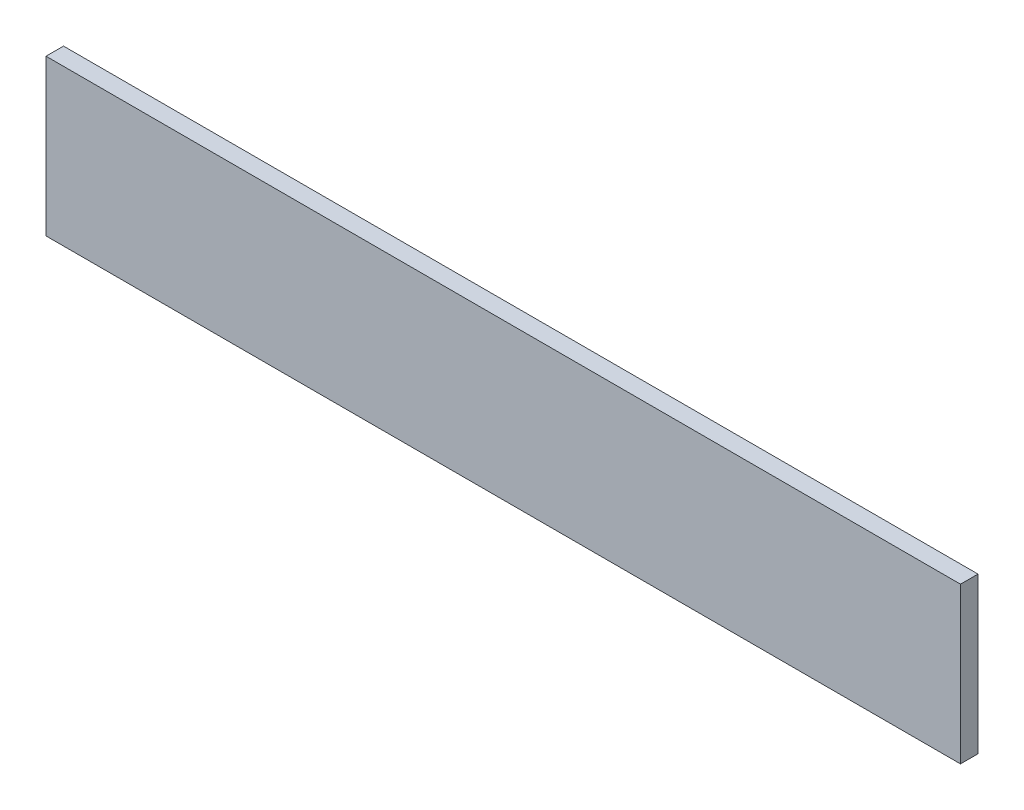
SolidWorks part; units mm, degrees
ref_plane "Płaszczyzna przednia" through (0, 0, 0) normal (0, 0, 1) x (1, 0, 0)
ref_plane "Płaszczyzna górna" through (0, 0, 0) normal (0, 1, 0) x (1, 0, 0)
ref_plane "Płaszczyzna prawa" through (0, 0, 0) normal (1, 0, 0) x (0, 0, -1)
sketch "Szkic1" plane through (0, 0, 0) normal (0, 0, 1) x (1, 0, 0)
  line L1 (0, 0) -> (470, 0)
  line L2 (0, 0) -> (0, 80)
  line L3 (0, 80) -> (470, 80)
  line L4 (470, 0) -> (470, 80)
  dimension "D1" = 470
  dimension "D2" = 80
extrude "Dodanie-wyciągnięcie1" add sketch "Szkic1" against normal blind 9
